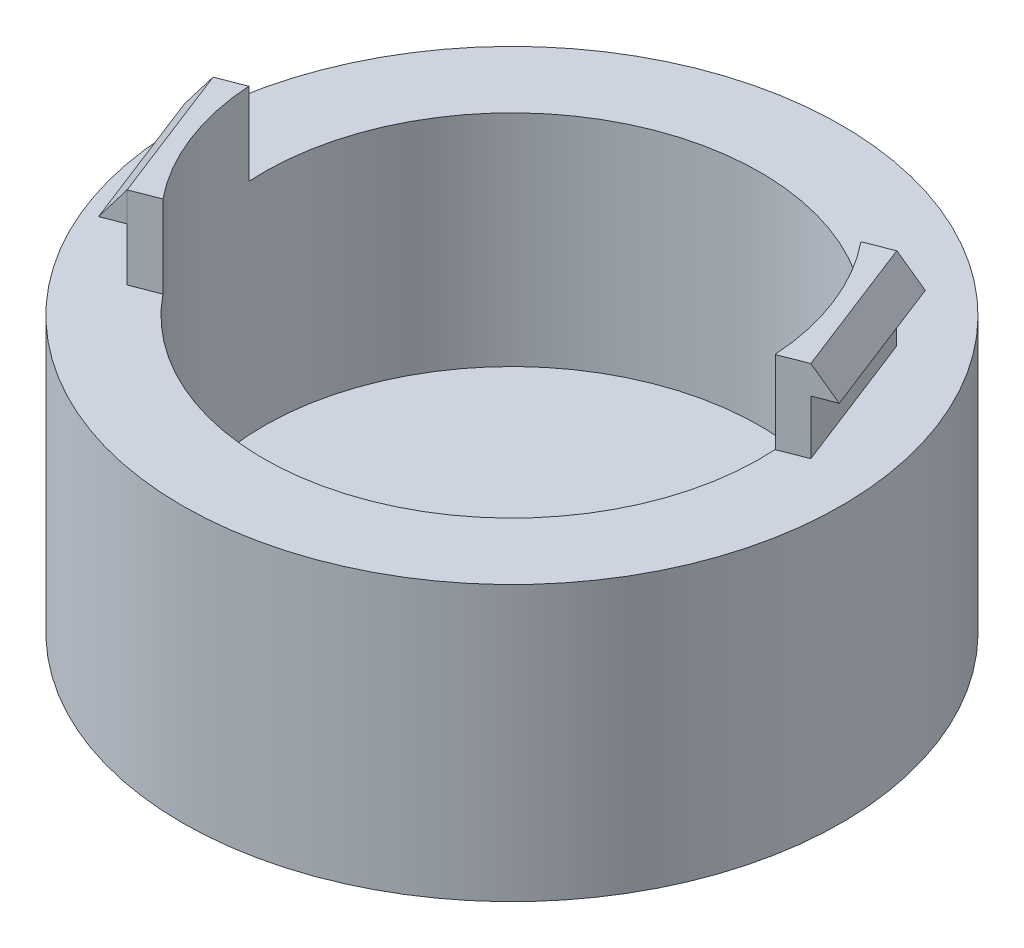
SolidWorks part; units mm, degrees
ref_plane "Front Plane" through (0, 0, 0) normal (0, 0, 1) x (1, 0, 0)
ref_plane "Top Plane" through (0, 0, 0) normal (0, 1, 0) x (1, 0, 0)
ref_plane "Right Plane" through (0, 0, 0) normal (1, 0, 0) x (0, 0, -1)
sketch "Sketch1" plane through (0, 0, 0) normal (0, 1, 0) x (1, 0, 0)
  circle A0 centre (0, 0) radius 15.24
  dimension "D1" = 30.48
extrude "Boss-Extrude1" add sketch "Sketch1" along normal blind 12.7 contours A0
sketch "Sketch3" plane through (0, 12.7, 0) normal (0, 1, 0) x (1, 0, 0)
  line L0 (12.6455, 1.1752) -> (-12.6455, -1.1752)
  line L1 (10.117, 7.677) -> (-10.117, -7.677)
  line L2 (12.6455, 1.1752) -> (10.117, 7.677)
  line L3 (12.6455, 1.1752) -> (11.4619, 0.7149)
  line L4 (10.117, 7.677) -> (8.9333, 7.2167)
  line L5 (11.4619, 0.7149) -> (8.9333, 7.2167)
  line L6 (-10.117, -7.677) -> (-12.6455, -1.1752)
  line L7 (-10.117, -7.677) -> (-8.8695, -7.1919)
  line L8 (-12.6455, -1.1752) -> (-11.3981, -0.6901)
  line L9 (-8.8695, -7.1919) -> (-11.3981, -0.6901)
  circle A0 centre (0, 0) radius 12.7
  circle A1 centre (0, 0) radius 11.477
  point P6 (0, 0)
  point P10 (0, 0)
  dimension "D1" = 22.954
  dimension "D2" = 25.4
  dimension "D3" = 1.27
  dimension "D4" = 6.9762
  dimension "D5" = 1.3384
extrude "Boss-Extrude10" add sketch "Sketch3" along normal blind 3.81 contours A1 L0 L2 L1 | A1 L1 L4 L5 | A1 L5 L3 L0 | A1 L1 L7 | A1 L0 L6 L1 | A1 L8 L0
sketch "Sketch6" plane through (-1.2643, 0, -3.2509) normal (-0.3625, 0, -0.932) x (-0.932, 0, 0.3625)
  line L0 (12.2116, 16.51) -> (12.2116, 15.1579)
  line L1 (12.2116, 16.51) -> (12.2116, 12.7) construction
  line L2 (12.2116, 15.1579) -> (13.2276, 15.1579)
  line L3 (13.2276, 15.1579) -> (12.2116, 16.51)
  dimension "D1" = 1.016
  dimension "D2" = 1.6913
extrude "Boss-Extrude11" add sketch "Sketch6" against normal blind 6.9893
sketch "Sketch7" plane through (1.2643, 0, 3.2509) normal (0.3625, 0, 0.932) x (0.932, 0, -0.3625)
  line L0 (12.2116, 16.51) -> (12.2116, 15.2076)
  line L1 (12.2116, 16.51) -> (12.2116, 12.7) construction
  line L2 (12.2116, 15.2076) -> (13.2276, 15.2076)
  line L3 (13.2276, 15.2076) -> (12.2116, 16.51)
  dimension "D1" = 1.3024
  dimension "D2" = 1.016
extrude "Boss-Extrude12" add sketch "Sketch7" against normal blind 6.985
sketch "Sketch9" plane through (0, 12.7, 0) normal (0, 1, 0) x (1, 0, 0)
  circle A0 centre (0, 0) radius 11.477
extrude "Cut-Extrude3" cut sketch "Sketch9" against normal blind 10.16
